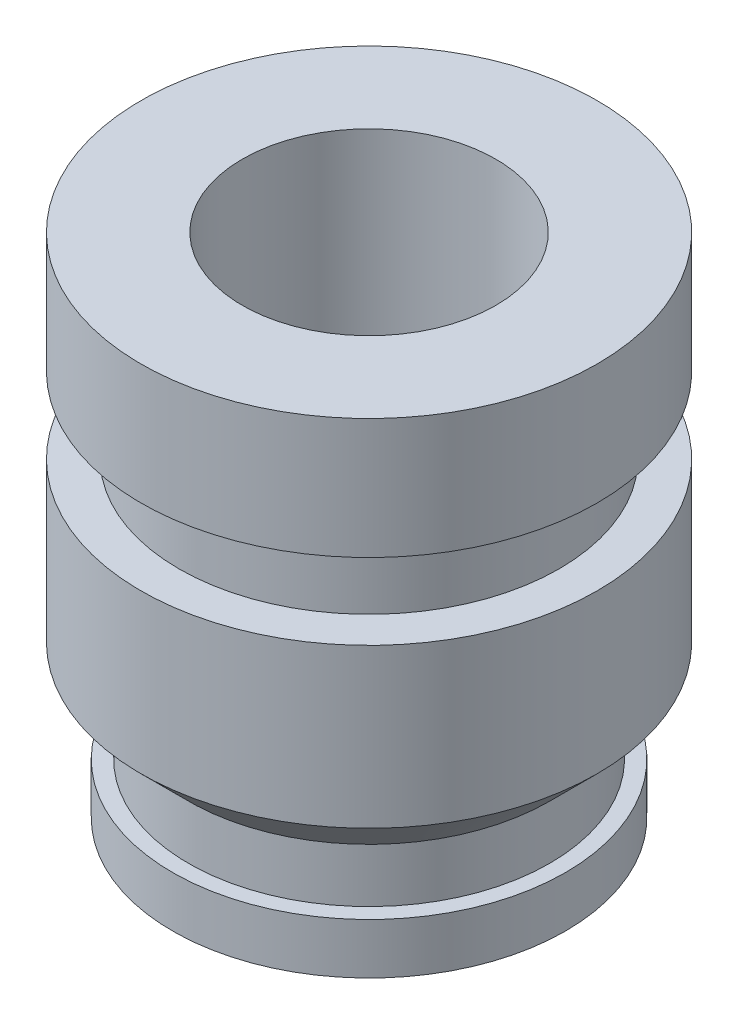
SolidWorks part; units mm, degrees
ref_plane "Front Plane" through (0, 0, 0) normal (0, 0, 1) x (1, 0, 0)
ref_plane "Top Plane" through (0, 0, 0) normal (0, 1, 0) x (1, 0, 0)
ref_plane "Right Plane" through (0, 0, 0) normal (1, 0, 0) x (0, 0, -1)
sketch "Sketch1" plane through (0, 0, 0) normal (0, 0, 1) x (1, 0, 0)
  line L0 (1, 0) -> (1, 4)
  line L1 (1, 4) -> (1.8, 4)
  line L2 (1.8, 4) -> (1.8, 3.05)
  line L3 (1.8, 3.05) -> (1.5, 3.05)
  line L4 (1.5, 3.05) -> (1.5, 2.45)
  line L5 (1.5, 2.45) -> (1.8, 2.45)
  line L6 (1.8, 2.45) -> (1.8, 1.2)
  line L7 (1.8, 1.2) -> (1.425, 0.825)
  line L8 (1.425, 0.825) -> (1.425, 0.4)
  line L9 (1.425, 0.4) -> (1.55, 0.4)
  line L10 (1.55, 0.4) -> (1.55, 0)
  line L11 (1.55, 0) -> (1, 0)
  line L12 (0, -1000) -> (0, 49000) construction
  point P13 (1.4093, 1.12)
  point P16 (1.8, 1.5838)
  point P17 (0, 0)
  dimension "D1" = 4
  dimension "D2" = 2
  dimension "D3" = 3.6
  dimension "D4" = 3.1
  dimension "D5" = 135
  dimension "D6" = 0.4
  dimension "D7" = 0.8
  dimension "D8" = 2.85
  dimension "D9" = 0.6
  dimension "D10" = 0.95
  dimension "D11" = 3
revolve "Revolve1" add sketch "Sketch1" angle 360 about L12
